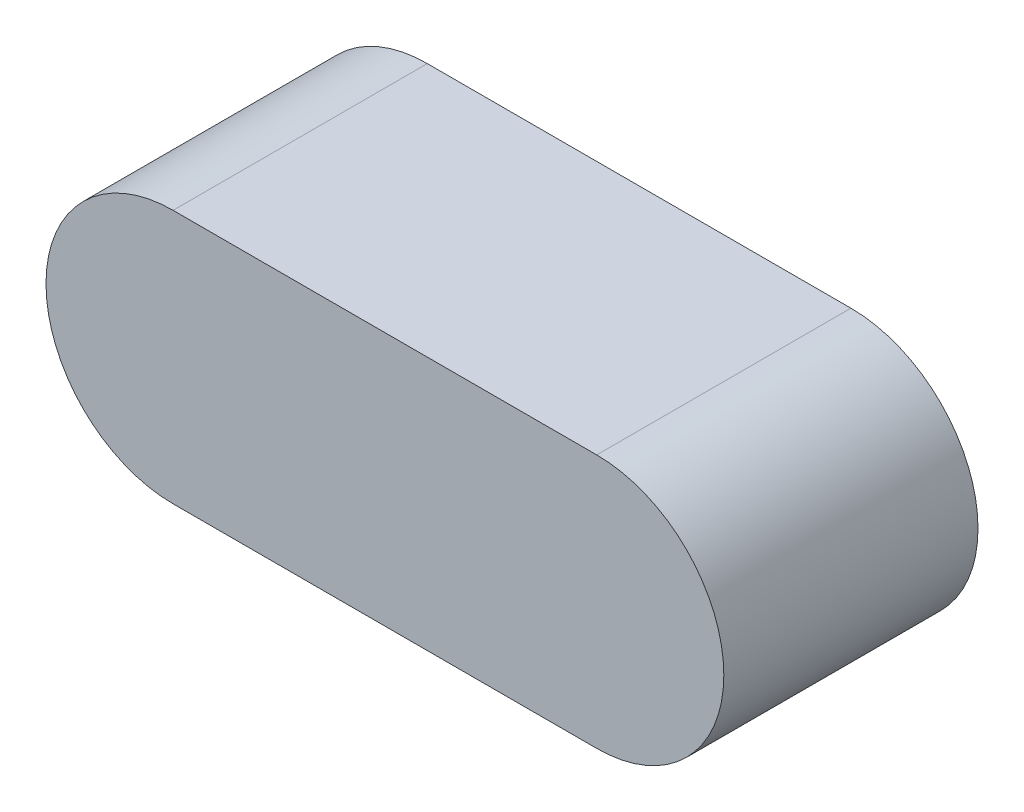
SolidWorks part; units mm, degrees
material "Alloy Steel (SS)"
ref_plane "Front Plane" through (0, 0, 0) normal (0, 0, 1) x (1, 0, 0)
ref_plane "Top Plane" through (0, 0, 0) normal (0, 1, 0) x (1, 0, 0)
ref_plane "Right Plane" through (0, 0, 0) normal (1, 0, 0) x (0, 0, -1)
sketch "Sketch1" plane through (0, 0, 0) normal (0, 0, 1) x (1, 0, 0)
  line L0 (0, 0) -> (10, 0) construction
  line L1 (0, 3) -> (10, 3)
  line L2 (0, -3) -> (10, -3)
  arc A0 (0, 3) -> (0, -3) centre (0, 0) ccw
  arc A1 (10, -3) -> (10, 3) centre (10, 0) ccw
  point P3 (5, 0)
  dimension "D1" = 10
  dimension "D2" = 6
extrude "Boss-Extrude1" add sketch "Sketch1" along normal blind 6
